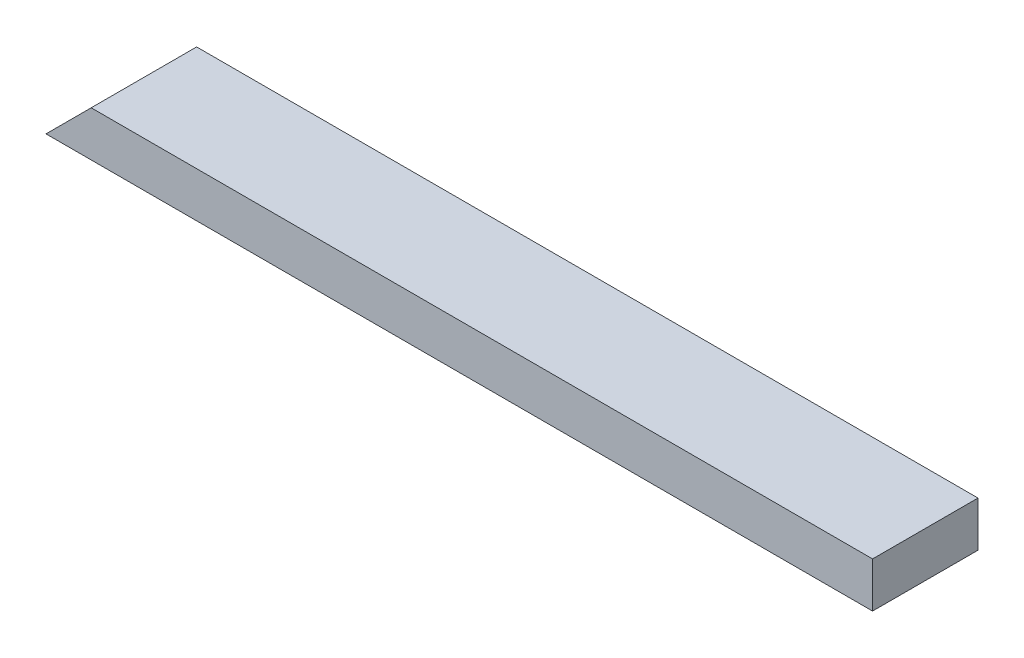
SolidWorks part; units mm, degrees
material "Pine"
ref_plane "Front Plane" through (0, 0, 0) normal (0, 0, 1) x (1, 0, 0)
ref_plane "Top Plane" through (0, 0, 0) normal (0, 1, 0) x (1, 0, 0)
ref_plane "Right Plane" through (0, 0, 0) normal (1, 0, 0) x (0, 0, -1)
sketch "Sketch1" plane through (0, 0, 0) normal (0, 1, 0) x (1, 0, 0)
  line L1 (0, 0) -> (696.9125, 0)
  line L2 (0, 0) -> (0, 88.9)
  line L3 (0, 88.9) -> (696.9125, 88.9)
  line L4 (696.9125, 0) -> (696.9125, 88.9)
  dimension "D1" = 88.9
  dimension "D2" = 696.9125
extrude "Boss-Extrude1" add sketch "Sketch1" along normal blind 38.1
sketch "Sketch2" plane through (0, 0, 0) normal (0, 0, 1) x (1, 0, 0)
  line L0 (0, 0) -> (38.1, 38.1)
  line L1 (0, 38.1) -> (696.9125, 38.1) construction
  line L2 (38.1, 38.1) -> (0, 38.1)
  line L3 (0, 38.1) -> (0, 0)
  dimension "D1" = 38.1
  dimension "D2" = 38.1
extrude "Cut-Extrude1" cut sketch "Sketch2" against normal through all
